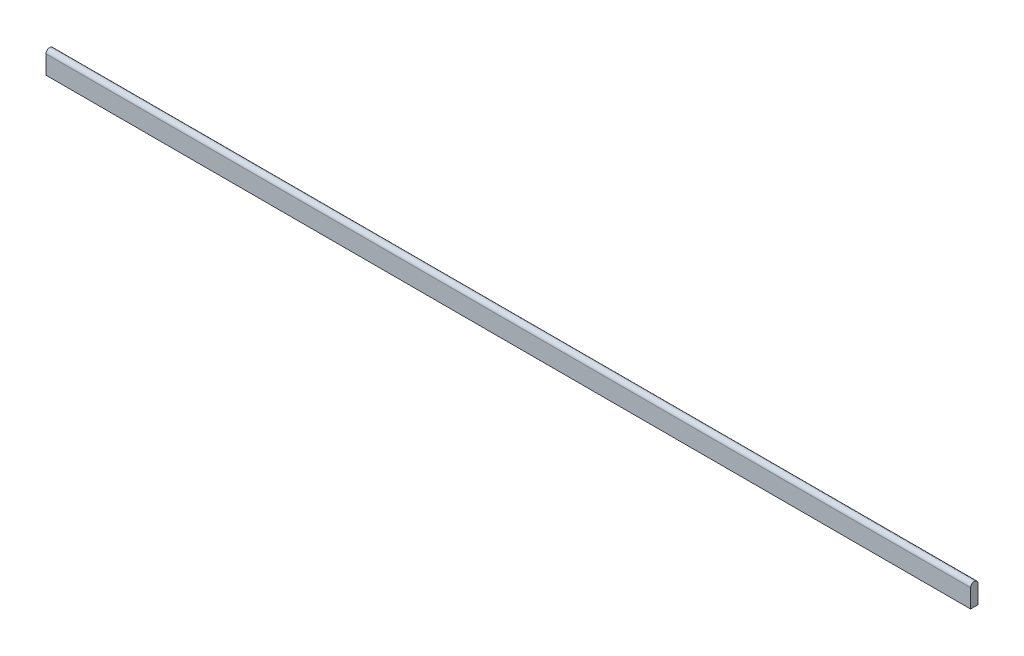
SolidWorks part; units mm, degrees
ref_plane "Plan de face" through (0, 0, 0) normal (0, 0, 1) x (1, 0, 0)
ref_plane "Plan de dessus" through (0, 0, 0) normal (0, 1, 0) x (1, 0, 0)
ref_plane "Plan de droite" through (0, 0, 0) normal (1, 0, 0) x (0, 0, -1)
sketch "Esquisse1" plane through (0, 0, 0) normal (1, 0, 0) x (0, 0, -1)
  line L0 (-2, 0) -> (-2, -10)
  line L1 (-2, -10) -> (2, -10)
  line L2 (2, -10) -> (2, 0)
  arc A0 (-2, 0) -> (2, 0) centre (0, 0) cw
  dimension "D1" = 2
  dimension "D2" = 10
extrude "Extrusion1" add sketch "Esquisse1" along normal blind 500
